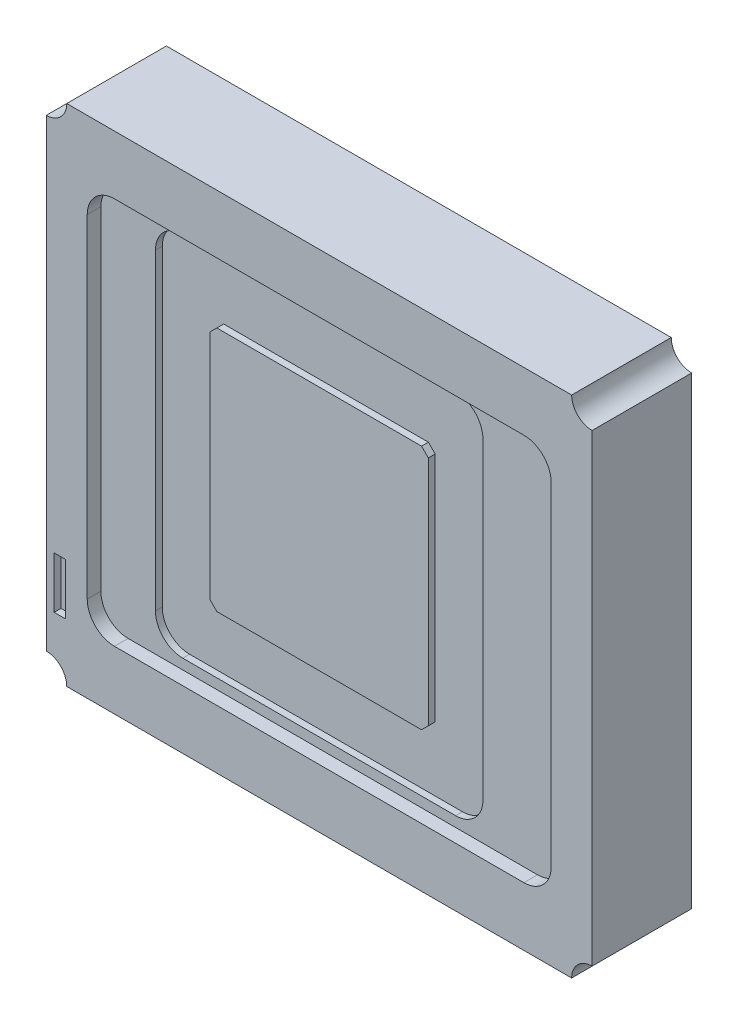
SolidWorks part; units mm, degrees
ref_plane "Front Plane" through (0, 0, 0) normal (0, 0, 1) x (1, 0, 0)
ref_plane "Top Plane" through (0, 0, 0) normal (0, 1, 0) x (1, 0, 0)
ref_plane "Right Plane" through (0, 0, 0) normal (1, 0, 0) x (0, 0, -1)
sketch "Sketch1" plane through (0, 0, 0) normal (0, 0, 1) x (1, 0, 0)
  line L1 (0, 0) -> (4, 0)
  line L2 (0, 0) -> (0, 3.7)
  line L3 (0, 3.7) -> (4, 3.7)
  line L4 (4, 0) -> (4, 3.7)
  dimension "D1" = 4
  dimension "D2" = 3.7
extrude "Boss-Extrude1" add sketch "Sketch1" along normal blind 0.73
sketch "Sketch2" plane through (0, 0, 0.73) normal (0, 0, 1) x (1, 0, 0)
  line L0 (4, 3.7) -> (0, 3.7) construction
  line L1 (0, 3.7) -> (0, 0) construction
  line L2 (0.15, 3.7) -> (0, 3.7)
  line L3 (0, 3.7) -> (0, 3.55)
  arc A0 (0.15, 3.7) -> (0, 3.55) centre (0, 3.7) cw
  dimension "D1" = 0.15
extrude "Cut-Extrude1" cut sketch "Sketch2" against normal blind 0.73
ref_plane "Plane3" through (0, 1.85, 0) normal (0, -1, 0) x (-1, 0, 0)
ref_plane "Plane4" through (2, 0, 0) normal (-1, 0, 0) x (0, 0, 1)
mirror "Mirror1" about plane through (0, 1.85, 0) normal (0, -1, 0) of "Cut-Extrude1"
mirror "Mirror2" about plane through (2, 0, 0) normal (-1, 0, 0) of "Mirror1", "Cut-Extrude1"
sketch "Sketch3" plane through (0, 0, 0.73) normal (0, 0, 1) x (1, 0, 0)
  line L0 (2, 3.7) -> (2, 0) construction
  line L1 (0.3, 3.27) -> (3.7, 3.27)
  line L2 (0.3, 3.27) -> (0.3, 0.43)
  line L3 (0.3, 0.43) -> (3.7, 0.43)
  line L4 (3.7, 3.27) -> (3.7, 0.43)
  line L5 (3.85, 3.7) -> (0.15, 3.7) construction
  line L6 (0.15, 0) -> (3.85, 0) construction
  line L8 (0, 3.55) -> (0, 0.15) construction
  line L9 (0, 1.85) -> (3.7, 1.85) construction
  point P10 (2, 3.27)
  point P15 (0.3, 1.85)
  dimension "D1" = 2.84
  dimension "D2" = 3.4
extrude "Cut-Extrude2" cut sketch "Sketch3" against normal blind 0.1
fillet "Fillet1" radius 0.2 4 edges at (0.3, 0.43, 0.68) (3.7, 0.43, 0.68) (3.7, 3.27, 0.68) (0.3, 3.27, 0.68)
sketch "Sketch4" plane through (0, 0, 0.73) normal (0, 0, 1) x (1, 0, 0)
  line L1 (0.0579, 0.4246) -> (0.141, 0.4246)
  line L2 (0.0579, 0.4246) -> (0.0579, 0.802)
  line L3 (0.0579, 0.802) -> (0.141, 0.802)
  line L4 (0.141, 0.4246) -> (0.141, 0.802)
extrude "Cut-Extrude3" cut sketch "Sketch4" against normal blind 0.05
sketch "Sketch6" plane through (0, 0, 0.63) normal (0, 0, 1) x (1, 0, 0)
  line L0 (0.3, 1.85) -> (3.7, 1.85) construction
  line L1 (0.7, 3.195) -> (3.1, 3.195)
  line L2 (0.7, 3.195) -> (0.7, 0.505)
  line L3 (0.7, 0.505) -> (3.1, 0.505)
  line L4 (3.1, 3.195) -> (3.1, 0.505)
  line L5 (0.3, 3.07) -> (0.3, 0.63) construction
  line L6 (3.7, 0.63) -> (3.7, 3.07) construction
  point P10 (0.7, 1.85)
  dimension "D1" = 2.69
  dimension "D2" = 0.6
  dimension "D3" = 0.4
extrude "Cut-Extrude4" cut sketch "Sketch6" against normal blind 0.05
fillet "Fillet2" radius 0.2 4 edges at (3.1, 3.195, 0.605) (3.1, 0.505, 0.605) (0.7, 0.505, 0.605) (0.7, 3.195, 0.605)
sketch "Sketch7" plane through (0, 0, 0.58) normal (0, 0, 1) x (1, 0, 0)
  line L0 (1.9, 3.195) -> (1.9, 0.505) construction
  line L1 (1.1, 2.7256) -> (2.7, 2.7256)
  line L2 (1.1, 2.7256) -> (1.1, 0.9256)
  line L3 (1.1, 0.9256) -> (2.7, 0.9256)
  line L4 (2.7, 2.7256) -> (2.7, 0.9256)
  line L5 (2.9, 3.195) -> (0.9, 3.195) construction
  line L6 (0.9, 0.505) -> (2.9, 0.505) construction
  point P10 (1.9, 2.7256)
  dimension "D1" = 1.8
  dimension "D2" = 1.6
extrude "Boss-Extrude2" add sketch "Sketch7" along normal blind 0.05
chamfer "Chamfer1" distance 0.05 angle 45 4 edges at (1.1, 2.7256, 0.605) (2.7, 2.7256, 0.605) (1.1, 0.9256, 0.605) (2.7, 0.9256, 0.605)
